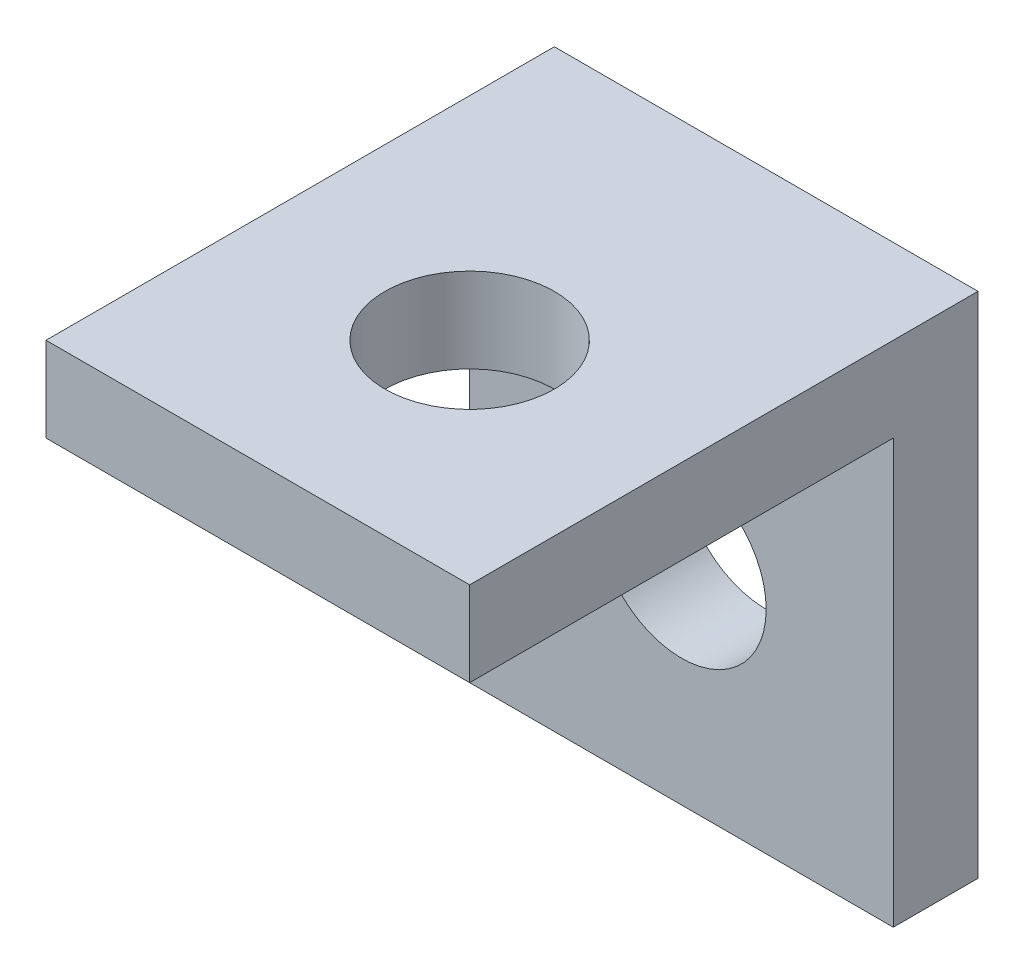
SolidWorks part; units mm, degrees
ref_plane "Alzado" through (0, 0, 0) normal (0, 0, 1) x (1, 0, 0)
ref_plane "Planta" through (0, 0, 0) normal (0, 1, 0) x (1, 0, 0)
ref_plane "Vista lateral" through (0, 0, 0) normal (1, 0, 0) x (0, 0, -1)
sketch "Sketch1" plane through (0, 0, 0) normal (0, 0, 1) x (1, 0, 0)
  line L1 (-5.3416, 3.5559) -> (-0.3416, 3.5559)
  line L2 (-5.3416, 3.5559) -> (-5.3416, -1.4441)
  line L3 (-5.3416, -1.4441) -> (-0.3416, -1.4441)
  line L4 (-0.3416, 3.5559) -> (-0.3416, -1.4441)
  dimension "D1" = 5
  dimension "D2" = 5
extrude "Boss-Extrude1" add sketch "Sketch1" along normal blind 1
sketch "Sketch2" plane through (0, 0, 1) normal (0, 0, 1) x (1, 0, 0)
  line L0 (-0.3416, -1.4441) -> (-0.3416, 3.5559) construction
  line L1 (-5.3416, 3.5559) -> (-0.3416, 3.5559)
  line L2 (-5.3416, 3.5559) -> (-5.3416, 2.5559)
  line L3 (-5.3416, 2.5559) -> (-0.3416, 2.5559)
  line L4 (-0.3416, 3.5559) -> (-0.3416, 2.5559)
  dimension "D1" = 1
extrude "Boss-Extrude2" add sketch "Sketch2" along normal blind 5
sketch "Sketch3" plane through (0, -1.4441, 0) normal (0, -1, 0) x (1, 0, 0)
  line L0 (-5.3416, 0) -> (-0.3416, 0) construction
  line L1 (-0.3416, 1) -> (-5.3416, 1)
  line L2 (-0.3416, 1) -> (-0.3416, 0)
  line L3 (-0.3416, 0) -> (-5.3416, 0)
  line L4 (-5.3416, 1) -> (-5.3416, 0)
extrude "Boss-Extrude3" add sketch "Sketch3" along normal blind 1
sketch "Sketch4" plane through (0, 0, 1) normal (0, 0, 1) x (1, 0, 0)
  circle A0 centre (-2.8416, 0.0559) radius 1
extrude "Cut-Extrude1" cut sketch "Sketch4" against normal blind 1
sketch "Sketch5" plane through (0, 2.5559, 0) normal (0, -1, 0) x (1, 0, 0)
  circle A0 centre (-2.8416, 3.5) radius 1
extrude "Cut-Extrude2" cut sketch "Sketch5" against normal blind 1
